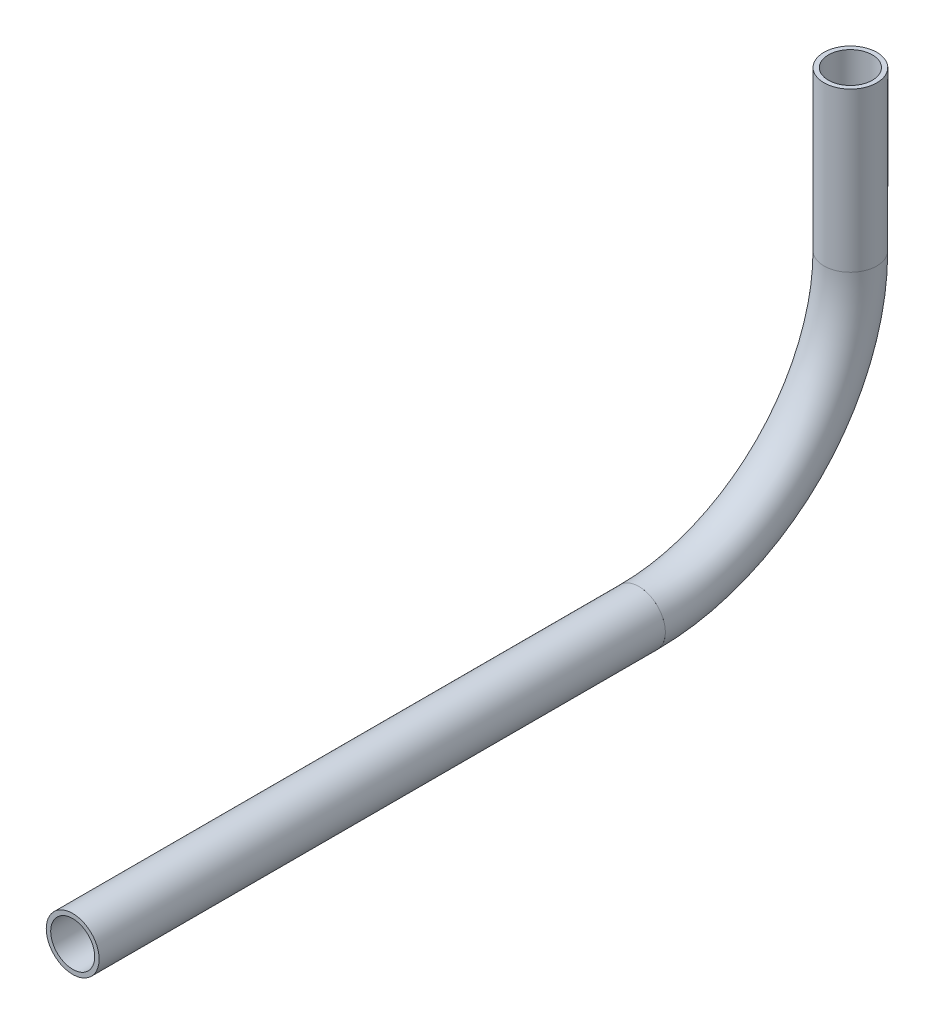
SolidWorks part; units mm, degrees
ref_plane "Front Plane" through (0, 0, 0) normal (0, 0, 1) x (1, 0, 0)
ref_plane "Top Plane" through (0, 0, 0) normal (0, 1, 0) x (1, 0, 0)
ref_plane "Right Plane" through (0, 0, 0) normal (1, 0, 0) x (0, 0, -1)
sketch "Sketch1" plane through (0, 0, 0) normal (1, 0, 0) x (0, 0, -1)
  line L0 (-303.1646, 599.96) -> (-167.159, 599.96)
  line L1 (-116.359, 650.76) -> (-116.359, 688.86)
  arc A0 (-167.159, 599.96) -> (-116.359, 650.76) centre (-167.159, 650.76) ccw
  dimension "D1" = 50.8
  dimension "D2" = 38.1
other "Pipe 0.5 SCH 40(1)"
ref_plane "Plane1" through (0, 599.96, 303.1646) normal (0, 0, -1) x (0, 1, 0)
sketch "Sketch11" plane through (0, 599.96, 303.1646) normal (0, 0, -1) x (0, 1, 0)
  circle A0 centre (0, 0) radius 5.2832
  circle A1 centre (0, 0) radius 6.35
  point P5 (0, 0)
  dimension "In_dia" = 10.5664
  dimension "Out_dia" = 12.7
